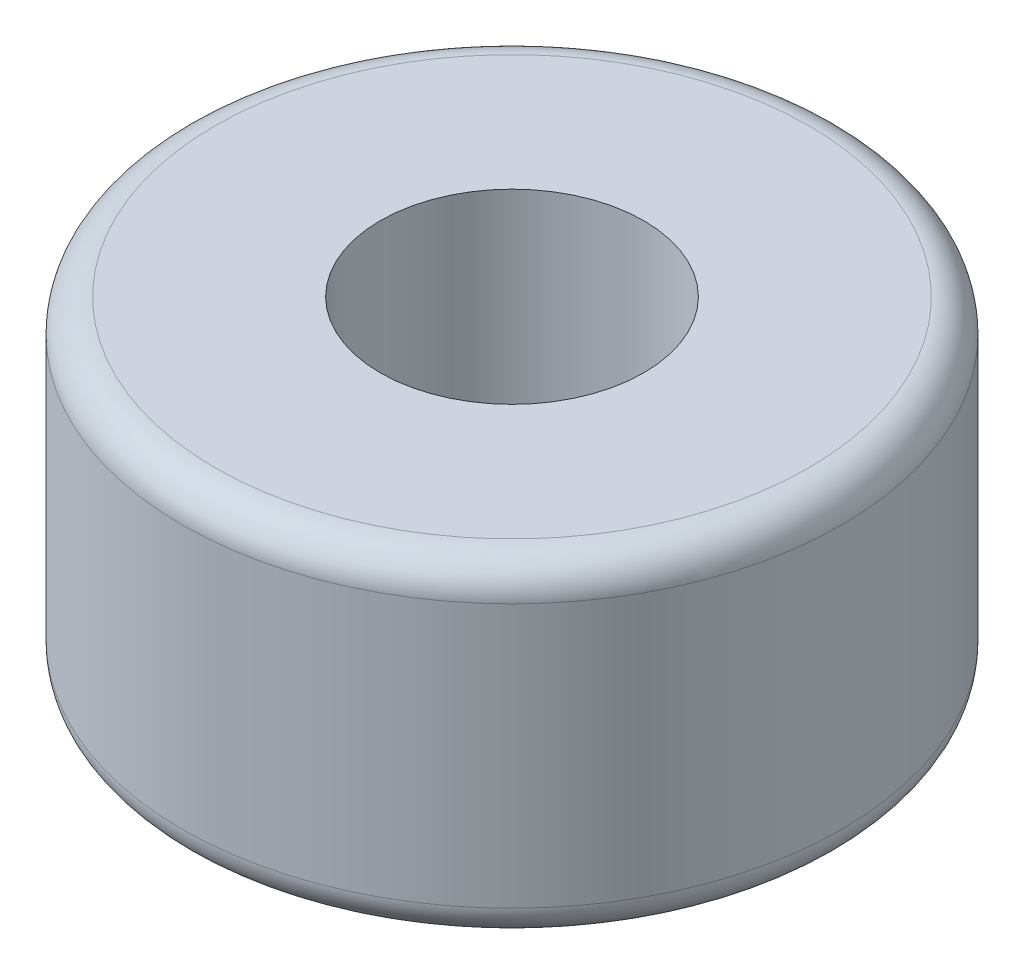
SolidWorks part; units mm, degrees
ref_plane "Front Plane" through (0, 0, 0) normal (0, 0, 1) x (1, 0, 0)
ref_plane "Top Plane" through (0, 0, 0) normal (0, 1, 0) x (1, 0, 0)
ref_plane "Right Plane" through (0, 0, 0) normal (1, 0, 0) x (0, 0, -1)
sketch "Sketch1" plane through (0, 0, 0) normal (0, 1, 0) x (1, 0, 0)
  circle A0 centre (0, 0) radius 4
  circle A1 centre (0, 0) radius 10
  dimension "D1" = 8
  dimension "D2" = 20
extrude "Boss-Extrude1" add sketch "Sketch1" along normal blind 10
fillet "Fillet1" radius 1 2 edges at (0, 0, 10) (0, 10, 10)
